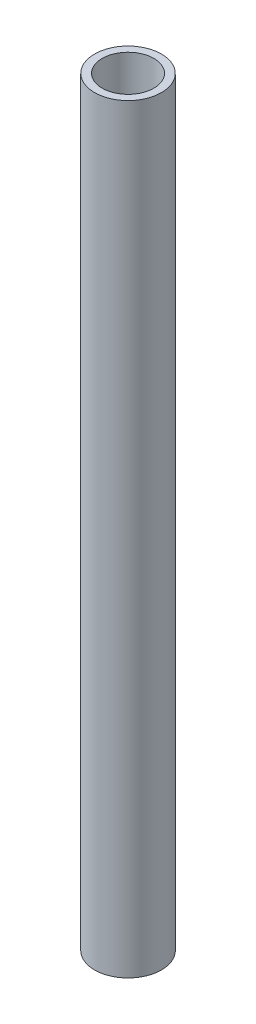
SolidWorks part; units mm, degrees
ref_plane "Спереди" through (0, 0, 0) normal (0, 0, 1) x (1, 0, 0)
ref_plane "Сверху" through (0, 0, 0) normal (0, 1, 0) x (1, 0, 0)
ref_plane "Справа" through (0, 0, 0) normal (1, 0, 0) x (0, 0, -1)
sketch "Эскиз1" plane through (0, 0, 0) normal (0, 1, 0) x (1, 0, 0)
  circle A0 centre (0, 0) radius 10.2
extrude "Вытянуть-Тонкостенный1" add sketch "Эскиз1" along normal blind 300 thin
